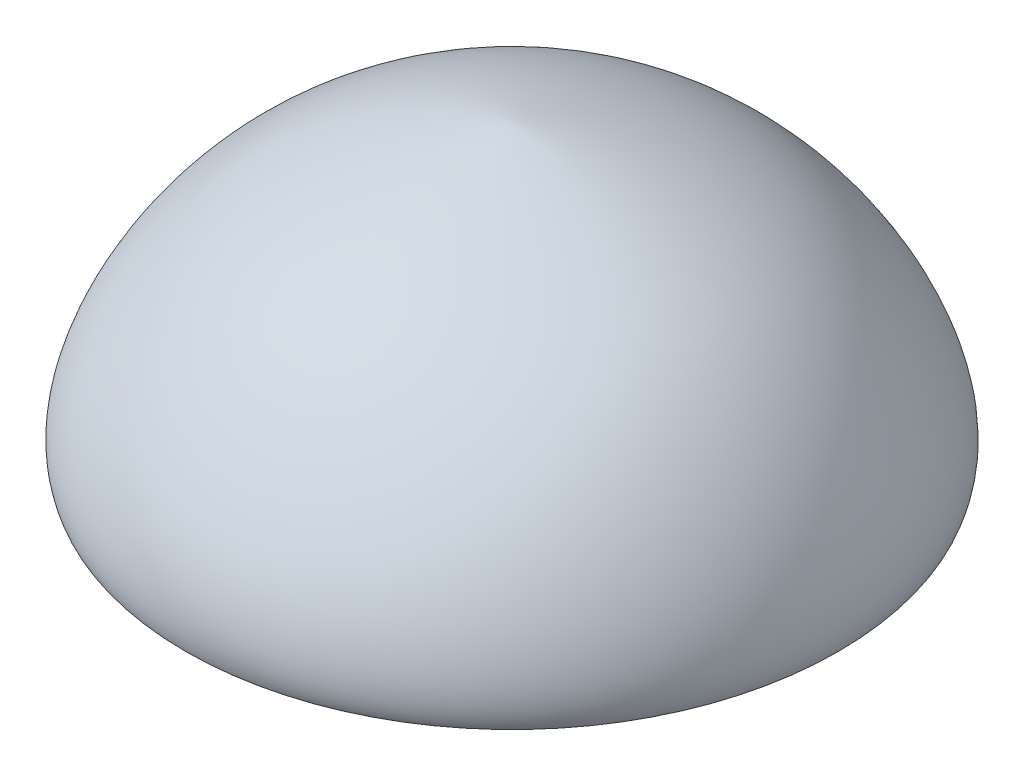
SolidWorks part; units mm, degrees
ref_plane "Front Plane" through (0, 0, 0) normal (0, 0, 1) x (1, 0, 0)
ref_plane "Top Plane" through (0, 0, 0) normal (0, 1, 0) x (1, 0, 0)
ref_plane "Right Plane" through (0, 0, 0) normal (1, 0, 0) x (0, 0, -1)
sketch "Sketch1" plane through (0, 0, 0) normal (0, 0, 1) x (1, 0, 0)
  line L0 (0, 0.45) -> (0, 0)
  line L1 (0, 0) -> (0.5, 0)
  line L2 (0, 0.45) -> (-0.2263, 0.45) construction
  line L3 (0.5, 0) -> (0.4442, -0.1368) construction
  spline S0 degree 3 poles (0.5, 0) (0.5254, 0.0623) (0.3897, 0.3789) (0.0255, 0.45) (0, 0.45) knots 0 0 0 0 0.503823 1 1 1 1
  dimension "D1" = 0.45
  dimension "D2" = 0.5
revolve "Revolve1" add sketch "Sketch1" angle 360 about L0
